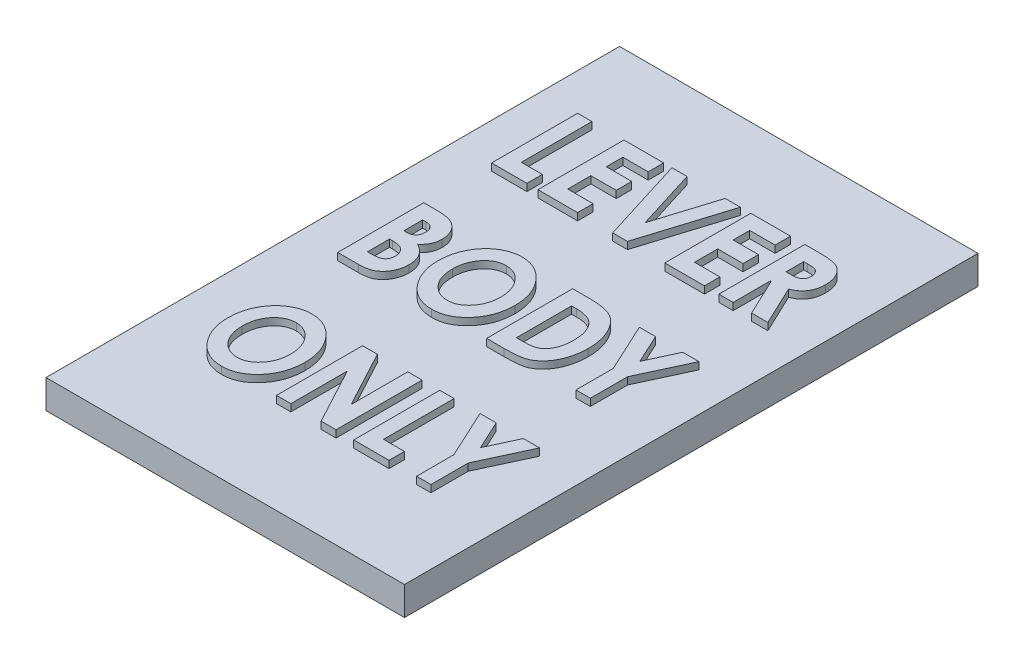
SolidWorks part; units mm, degrees
ref_plane "Front Plane" through (0, 0, 0) normal (0, 0, 1) x (1, 0, 0)
ref_plane "Top Plane" through (0, 0, 0) normal (0, 1, 0) x (1, 0, 0)
ref_plane "Right Plane" through (0, 0, 0) normal (1, 0, 0) x (0, 0, -1)
sketch "Sketch1" plane through (0, 0, 0) normal (0, 1, 0) x (1, 0, 0)
  line L1 (9.7, -17.2) -> (-9.7, -17.2)
  line L2 (9.7, -17.2) -> (9.7, 17.2)
  line L3 (9.7, 17.2) -> (-9.7, 17.2)
  line L4 (-9.7, -17.2) -> (-9.7, 17.2)
  line L5 (9.7, -17.2) -> (-9.7, 17.2) construction
  line L6 (9.7, 17.2) -> (-9.7, -17.2) construction
  point P0 (0, 0)
  dimension "D1" = 19.4
  dimension "D2" = 34.4
extrude "Boss-Extrude1" add sketch "Sketch1" along normal blind 2
sketch "Sketch2" plane through (0, 2, 0) normal (0, 1, 0) x (1, 0, 0)
  line L1 (12.5, -20) -> (-12.5, -20)
  line L2 (12.5, -20) -> (12.5, 20)
  line L3 (12.5, 20) -> (-12.5, 20)
  line L4 (-12.5, -20) -> (-12.5, 20)
  line L5 (12.5, -20) -> (-12.5, 20) construction
  line L6 (12.5, 20) -> (-12.5, -20) construction
  point P0 (0, 0)
  dimension "D1" = 25
  dimension "D2" = 40
extrude "Boss-Extrude2" add sketch "Sketch2" along normal blind 2
sketch "Sketch3" plane through (0, 4, 0) normal (0, 1, 0) x (1, 0, 0)
  line L0 (-12.5, 8) -> (12.5, 8) construction
  line L1 (-12.5, 20) -> (-12.5, -20) construction
  line L2 (12.5, -20) -> (12.5, 20) construction
  line L3 (12.5, 20) -> (-12.5, 20) construction
  text T0 "<b>LEVER</b>\r\n<b>BODY</b>\r\n<b>ONLY</b>" font "Century Gothic" height 6
  dimension "D1" = 12
extrude "Boss-Extrude3" add sketch "Sketch3" along normal blind 0.5
